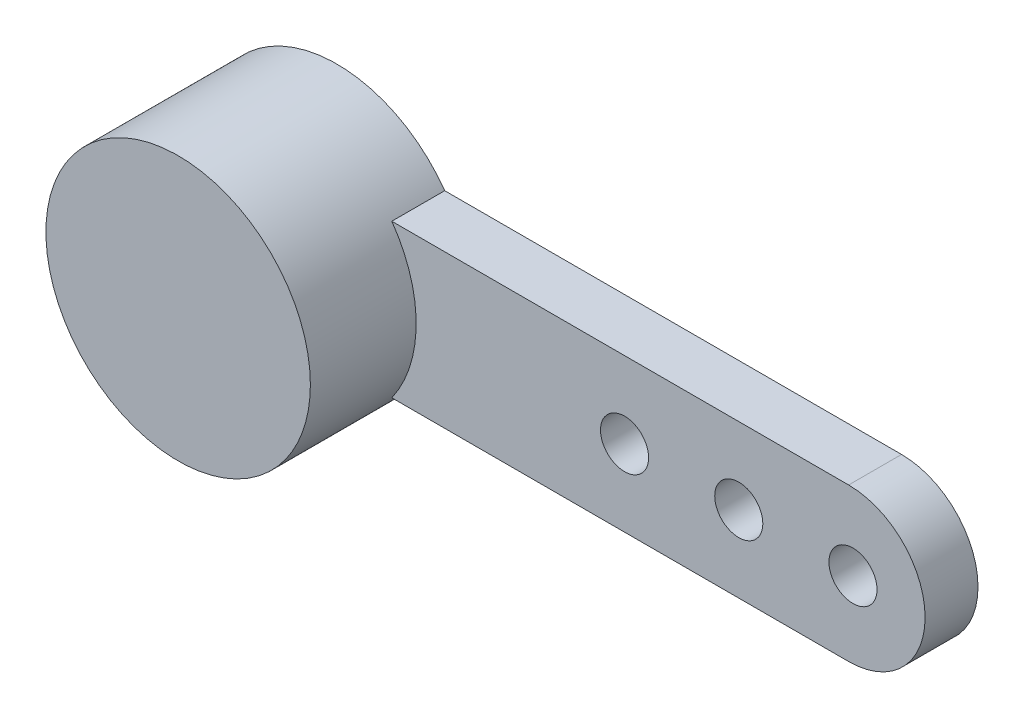
SolidWorks part; units mm, degrees
ref_plane "Plan de face" through (0, 0, 0) normal (0, 0, 1) x (1, 0, 0)
ref_plane "Plan de dessus" through (0, 0, 0) normal (0, 1, 0) x (1, 0, 0)
ref_plane "Plan de droite" through (0, 0, 0) normal (1, 0, 0) x (0, 0, -1)
sketch "Sketch1" plane through (0, 0, 0) normal (0, 0, 1) x (1, 0, 0)
  line L0 (2.2437, 1.59) -> (11.7437, 1.59)
  line L2 (11.7437, -1.59) -> (2.2437, -1.59)
  arc A0 (2.2437, 1.59) -> (2.2437, -1.59) centre (0, 0) ccw
  arc A1 (11.7437, 1.59) -> (11.7437, -1.59) centre (11.7437, 0) cw
  dimension "D1" = 5.5
  dimension "D2" = 9.5
  dimension "D3" = 3.18
  dimension "D4" = 1.59
extrude "Boss-Extrude1" add sketch "Sketch1" along normal blind 1.1
sketch "Sketch2" plane through (0, 0, 1.1) normal (0, 0, 1) x (1, 0, 0)
  circle A0 centre (0, 0) radius 2.75
  dimension "D1" = 5.5
extrude "Boss-Extrude2" add sketch "Sketch2" along normal blind 2.2
sketch "Sketch3" plane through (0, 0, 0) normal (0, 0, -1) x (-1, 0, 0)
  line L0 (-11.7437, 1.59) -> (-2.2437, 1.59) construction
  line L1 (-2.2437, -1.59) -> (-11.7437, -1.59) construction
  circle A0 centre (-11.8337, 0) radius 0.5
  circle A1 centre (-9.4587, 0) radius 0.5
  circle A2 centre (-7.0837, 0) radius 0.5
  arc A3 (-11.7437, 1.59) -> (-11.7437, -1.59) centre (-11.7437, 0) ccw construction
  point P6 (-13.3337, 0)
  dimension "D1" = 1
  dimension "D2" = 1
  dimension "D3" = 1
  dimension "D6" = 1.5
  dimension "D7" = 1.59
  dimension "D8" = 1.59
  dimension "D9" = 1.59
  dimension "D4" = 4.75
  dimension "D5" = 2.375
extrude "Cut-Extrude1" cut sketch "Sketch3" against normal up to next
